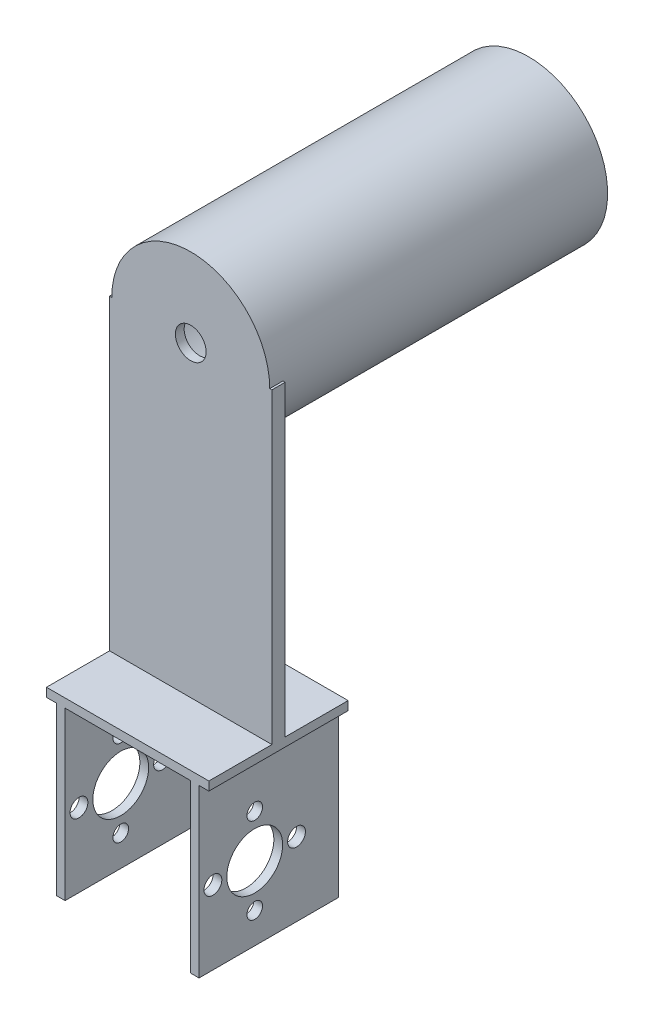
SolidWorks part; units mm, degrees
ref_plane "Front Plane" through (0, 0, 0) normal (0, 0, 1) x (1, 0, 0)
ref_plane "Top Plane" through (0, 0, 0) normal (0, 1, 0) x (1, 0, 0)
ref_plane "Right Plane" through (0, 0, 0) normal (1, 0, 0) x (0, 0, -1)
sketch "Sketch1" plane through (0, 0, 0) normal (0, 1, 0) x (1, 0, 0)
  line L0 (-3.0743, 1.2077) -> (-1.0743, 1.2077)
  line L1 (-3.0743, 1.2077) -> (-3.0743, -30.5323)
  line L2 (-1.0743, 1.2077) -> (-1.0743, -30.5323)
  line L3 (-3.0743, -30.5323) -> (-1.0743, -30.5323)
  line L4 (13.1897, 10.0004) -> (13.1897, -34.5364) construction
  line L5 (27.4537, 1.2077) -> (27.4537, -30.5323)
  line L6 (29.4537, -30.5323) -> (27.4537, -30.5323)
  line L7 (29.4537, 1.2077) -> (29.4537, -30.5323)
  line L8 (29.4537, 1.2077) -> (27.4537, 1.2077)
  dimension "D1" = 2
  dimension "D2" = 31.74
  dimension "D3" = 16.264
extrude "Boss-Extrude1" add sketch "Sketch1" along normal blind 40
ref_plane "Plane1" through (0, 40, 0) normal (0, 1, 0) x (1, 0, 0)
sketch "Sketch2" plane through (0, 40, 0) normal (0, 1, 0) x (1, 0, 0)
  line L0 (-5.3063, 1.2077) -> (31.6937, 1.2077)
  line L1 (-5.3063, 1.2077) -> (-5.3063, -30.5323)
  line L2 (31.6937, 1.2077) -> (31.6937, -30.5323)
  line L3 (-5.3063, -30.5323) -> (31.6937, -30.5323)
  line L4 (27.4537, -30.5323) -> (29.4537, -30.5323) construction
  line L5 (29.4537, 1.2077) -> (27.4537, 1.2077) construction
  line L6 (13.1937, -30.5323) -> (13.1937, 15.7517) construction
  line L7 (13.1937, 15.7517) -> (13.1937, -60.8234) construction
  line L8 (27.4537, 1.2077) -> (27.4537, -30.5323) construction
  line L9 (-1.0743, -30.5323) -> (-1.0743, 1.2077) construction
  dimension "D1" = 37
  dimension "D2" = 14.26
  dimension "D3" = 14.268
  dimension "D4" = 18.5
  dimension "D5" = 18.5
extrude "Boss-Extrude3" add sketch "Sketch2" against normal blind 2
sketch "Sketch8" plane through (0, 40, 0) normal (0, 1, 0) x (1, 0, 0)
  line L0 (-5.3063, -13.1623) -> (-5.3063, -16.1623)
  line L1 (-5.3063, -13.1623) -> (31.6937, -13.1623)
  line L2 (-5.3063, -16.1623) -> (31.6937, -16.1623)
  line L3 (31.6937, -13.1623) -> (31.6937, -16.1623)
  line L4 (-5.3063, 1.2077) -> (-5.3063, -30.5323) construction
  line L6 (31.6937, -30.5323) -> (31.6937, 1.2077) construction
  point P6 (-5.3063, -14.6623)
  dimension "D1" = 3
  dimension "D2" = 1.5
  dimension "D3" = 15.87
  dimension "D4" = 15.87
extrude "Boss-Extrude4" add sketch "Sketch8" along normal blind 70
sketch "Sketch12" plane through (0, 0, 13.1623) normal (0, 0, -1) x (-1, 0, 0)
  line L0 (-31.6937, 110) -> (5.3063, 110) construction
  circle A0 centre (-13.1937, 110) radius 18
extrude "Boss-Extrude6" add sketch "Sketch12" along normal blind 74 and the other way blind 3 contours A0
sketch "Sketch17" plane through (0, 0, -60.8377) normal (0, 0, -1) x (-1, 0, 0)
  line L0 (-31.1937, 110) -> (4.8063, 110) construction
  line L1 (-13.1937, 128) -> (-13.1937, 92) construction
  circle A0 centre (-13.1937, 110) radius 18 construction
  arc A1 (-31.1937, 110) -> (4.8063, 110) centre (-13.1937, 110) ccw construction
sketch "Sketch18" plane through (0, 0, -60.8377) normal (0, 0, -1) x (-1, 0, 0)
  line L0 (-31.1937, 110) -> (4.8063, 110) construction
  circle A0 centre (-13.1937, 110) radius 16.1
extrude "Cut-Extrude2" cut sketch "Sketch18" against normal blind 75
sketch "Sketch19" plane through (0, 0, 14.1623) normal (0, 0, -1) x (-1, 0, 0)
  line L0 (-31.1937, 110) -> (4.8063, 110) construction
  circle A0 centre (-13.1937, 110) radius 3.5
extrude "Cut-Extrude3" cut sketch "Sketch19" against normal blind 74
sketch "Sketch20" plane through (29.4537, 0, 0) normal (1, 0, 0) x (0, 0, -1)
  line L0 (-1026.1464, 0.0159) -> (48973.8536, 0.0159) construction
  line L2 (-1020.6004, 7.0009) -> (48979.3996, 7.0009)
  line L3 (1.2077, -967.9144) -> (1.2077, 49032.0856) construction
  line L4 (-1022.4653, 16.7799) -> (48977.5347, 16.7799)
  line L6 (-1017.7509, 26.5589) -> (48982.2491, 26.5589)
  line L7 (-8.3173, -967.0415) -> (-8.3173, 49032.9585)
  line L8 (-17.8423, -967.8053) -> (-17.8423, 49032.1947)
  line L10 (-27.3673, -967.9144) -> (-27.3673, 49032.0856)
  circle A0 centre (-17.8423, 16.7799) radius 6.36
  circle A1 centre (-17.8423, 26.5589) radius 1.78
  circle A2 centre (-17.8423, 7.0009) radius 1.78
  circle A3 centre (-27.3673, 16.7799) radius 2.03
  circle A4 centre (-8.3173, 16.7799) radius 2.03
  dimension "D7" = 9.779
  dimension "D1" = 6.985
  dimension "D2" = 26.543
  dimension "D3" = 16.764
  dimension "D4" = 9.525
  dimension "D5" = 19.05
  dimension "D6" = 28.575
  dimension "D8" = 9.779
  dimension "D9" = 9.525
  dimension "D10" = 9.525
sketch "Sketch22" plane through (29.4537, 0, 0) normal (1, 0, 0) x (0, 0, -1)
extrude "Cut-Extrude4" cut sketch "Sketch20" against normal through all both and the other way through all
